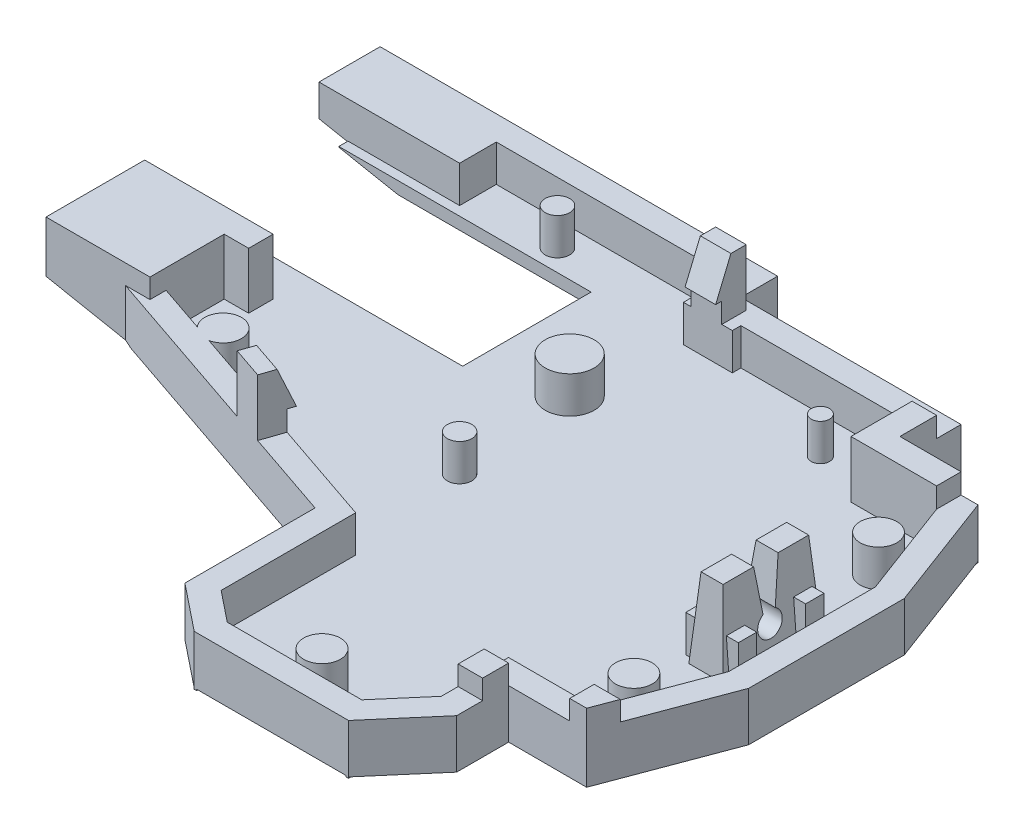
SolidWorks part; units mm, degrees
ref_plane "Front Plane" through (0, 0, 0) normal (0, 0, 1) x (1, 0, 0)
ref_plane "Top Plane" through (0, 0, 0) normal (0, 1, 0) x (1, 0, 0)
ref_plane "Right Plane" through (0, 0, 0) normal (1, 0, 0) x (0, 0, -1)
sketch "Sketch13" plane through (0, 0, 0) normal (0, 1, 0) x (1, 0, 0)
  line L1 (0, 0) -> (50, 0)
  line L2 (0, 0) -> (0, -45)
  line L3 (0, -45) -> (50, -45)
  line L4 (50, 0) -> (50, -45)
  dimension "D1" = 50
extrude "Boss-Extrude4" add sketch "Sketch13" along normal blind 1.6
sketch "Sketch14" plane through (0, 1.6, 0) normal (0, 1, 0) x (1, 0, 0)
  line L1 (50, 0) -> (40, 0)
  line L2 (50, 0) -> (50, -8)
  line L3 (50, -8) -> (40, -8)
  line L4 (40, 0) -> (40, -8)
extrude "Cut-Extrude6" cut sketch "Sketch14" against normal through all
sketch "Sketch15" plane through (0, 1.6, 0) normal (0, 1, 0) x (1, 0, 0)
  line L1 (40, 0) -> (22, 0)
  line L2 (40, 0) -> (40, -3)
  line L3 (40, -3) -> (22, -3)
  line L4 (22, 0) -> (22, -3)
extrude "Cut-Extrude7" cut sketch "Sketch15" against normal through all
sketch "Sketch16" plane through (0, 1.6, 0) normal (0, 1, 0) x (1, 0, 0)
  line L1 (22, -3) -> (26, -3)
  line L2 (22, -3) -> (22, -3.7)
  line L3 (22, -3.7) -> (26, -3.7)
  line L4 (26, -3) -> (26, -3.7)
  dimension "D1" = 0.7
  dimension "D2" = 4
extrude "Cut-Extrude8" cut sketch "Sketch16" against normal through all
sketch "Sketch17" plane through (0, 1.6, 0) normal (0, 1, 0) x (1, 0, 0)
  line L3 (40, -8) -> (50, -8) construction
  line L4 (47, -8) -> (50, -16)
  line L6 (50, -45) -> (50, -8) construction
  line L7 (50, -16) -> (65.8811, -16)
  line L8 (65.8811, -16) -> (65.8811, 17.9573)
  line L9 (65.8811, 17.9573) -> (47, 17.9573)
  line L10 (47, 17.9573) -> (47, -8)
extrude "Cut-Extrude9" cut sketch "Sketch17" against normal through all
sketch "Sketch18" plane through (0, 1.6, 0) normal (0, 1, 0) x (1, 0, 0)
  line L0 (40, -8) -> (40, -36) construction
  line L2 (40, -36) -> (61.1096, -36)
  line L3 (40, -36) -> (40, -58.8405)
  line L4 (40, -58.8405) -> (61.1096, -58.8405)
  line L5 (61.1096, -36) -> (61.1096, -58.8405)
extrude "Cut-Extrude10" cut sketch "Sketch18" against normal through all
sketch "Sketch21" plane through (0, 1.6, 0) normal (0, 1, 0) x (1, 0, 0)
  line L0 (50, -16) -> (27.9365, -16) construction
  line L1 (47, -36) -> (47, -28) construction
  line L2 (50, -36) -> (40, -36) construction
  line L3 (50, -28) -> (47, -36)
  line L4 (50, -36) -> (50, -16) construction
  line L5 (47, -36) -> (47, -49.2976)
  line L6 (47, -49.2976) -> (75.1968, -49.2976)
  line L7 (75.1968, -49.2976) -> (75.1968, -28)
  line L8 (75.1968, -28) -> (50, -28)
extrude "Cut-Extrude11" cut sketch "Sketch21" against normal through all
sketch "Sketch22" plane through (0, 1.6, 0) normal (0, 1, 0) x (1, 0, 0)
  line L0 (0, 0) -> (0, -19.3362) construction
  line L1 (0, 0) -> (0, -45) construction
  line L4 (0, -19.3362) -> (2, -19.3362)
  line L5 (0, -19.3362) -> (0, -22.3362)
  line L6 (0, -22.3362) -> (2, -22.3362)
  line L7 (2, -19.3362) -> (2, -22.3362)
  dimension "D1" = 2
  dimension "D2" = 3
extrude "Cut-Extrude12" cut sketch "Sketch22" against normal through all
sketch "Sketch23" plane through (0, 1.6, 0) normal (0, 1, 0) x (1, 0, 0)
  line L0 (40, -45) -> (23.5, -45) construction
  line L1 (0, -45) -> (40, -45) construction
  line L2 (23.5, -45) -> (23.5, -32)
  line L3 (0, -22.3362) -> (0, -26.3362) construction
  line L4 (0, -22.3362) -> (0, -45) construction
  line L5 (23.5, -32) -> (0, -26.3362)
  line L6 (0, -26.3362) -> (-30.2262, -26.3362)
  line L7 (-30.2262, -26.3362) -> (-30.2262, -63.1883)
  line L8 (-30.2262, -63.1883) -> (23.5, -63.1883)
  line L9 (23.5, -63.1883) -> (23.5, -45)
extrude "Cut-Extrude13" cut sketch "Sketch23" against normal through all
sketch "Sketch24" plane through (0, 1.6, 0) normal (0, 1, 0) x (1, 0, 0)
  line L0 (23.5, -43) -> (7.4911, -43)
  line L1 (23.5, -45) -> (40, -45) construction
  line L2 (7.4911, -43) -> (7.4911, -69.5502)
  line L3 (40, -36) -> (40, -45) construction
  line L4 (37, -45) -> (40, -41.5)
  line L5 (23.5, -45) -> (23.5, -32) construction
  line L6 (26, -45) -> (23.5, -43)
  line L7 (7.4911, -69.5502) -> (44.754, -69.5502)
  line L8 (44.754, -69.5502) -> (44.754, -41.5)
  line L9 (44.754, -41.5) -> (40, -41.5)
  line L10 (37, -45) -> (26, -45)
extrude "Cut-Extrude14" cut sketch "Sketch24" against normal through all
sketch "Sketch25" plane through (0, 1.6, 0) normal (0, 1, 0) x (1, 0, 0)
  line L0 (50, -22) -> (47.6007, -22.0598) construction
  line L1 (50, -28) -> (50, -16) construction
  line L2 (47.6007, -22.0598) -> (47.6007, -18.0598) construction
  line L4 (47.6007, -18.0598) -> (44.8007, -18.0598)
  line L5 (47.6007, -18.0598) -> (47.6007, -26.0598)
  line L6 (47.6007, -26.0598) -> (44.8007, -26.0598)
  line L7 (44.8007, -18.0598) -> (44.8007, -26.0598)
  dimension "D1" = 2.8
  dimension "D2" = 8
extrude "Cut-Extrude15" cut sketch "Sketch25" against normal through all
sketch "Sketch28" plane through (0, 0, 0) normal (0, -1, 0) x (1, 0, 0)
  line L44 (42, 38) -> (42, 42.2398)
  line L45 (42, 42.2398) -> (37.9199, 47)
  line L46 (37.9199, 47) -> (25.2984, 47)
  line L47 (25.2984, 47) -> (21.5, 43.9612)
  line L48 (21.5, 43.9612) -> (21.5, 33.5752)
  line L49 (21.5, 33.5752) -> (-2, 27.9115)
  line L50 (-2, 27.9115) -> (-2, -2)
  line L51 (-2, -2) -> (24, -2)
  line L52 (24, -2) -> (24, 1)
  line L53 (24, 1) -> (42, 1)
  line L54 (42, 1) -> (42, 6)
  line L55 (42, 6) -> (48.386, 6)
  line L56 (48.386, 6) -> (52, 15.6373)
  line L57 (52, 15.6373) -> (52, 28.3627)
  line L58 (52, 28.3627) -> (48.386, 38)
  line L59 (48.386, 38) -> (42, 38)
  line L60 (42, 38) -> (42, 42.2398)
  line L61 (42, 42.2398) -> (37.9199, 47)
  line L62 (37.9199, 47) -> (25.2984, 47)
  line L63 (25.2984, 47) -> (21.5, 43.9612)
  line L64 (21.5, 43.9612) -> (21.5, 33.5752)
  line L65 (21.5, 33.5752) -> (-2, 27.9115)
  line L66 (-2, 27.9115) -> (-2, -2)
  line L67 (-2, -2) -> (24, -2)
  line L68 (24, -2) -> (24, 1)
  line L69 (24, 1) -> (42, 1)
  line L70 (42, 1) -> (42, 6)
  line L71 (42, 6) -> (48.386, 6)
  line L72 (48.386, 6) -> (52, 15.6373)
  line L73 (52, 15.6373) -> (52, 28.3627)
  line L74 (52, 28.3627) -> (48.386, 38)
  line L75 (48.386, 38) -> (42, 38)
  dimension "D1" = 2
extrude "Boss-Extrude6" add sketch "Sketch28" along normal blind 6
sketch "Sketch30" plane through (0, 0, 0) normal (0, 1, 0) x (1, 0, 0)
  line L8 (44.8007, -18.0598) -> (44.8007, -26.0598)
  line L9 (44.8007, -26.0598) -> (47.6007, -26.0598)
  line L10 (47.6007, -26.0598) -> (47.6007, -18.0598)
  line L11 (47.6007, -18.0598) -> (44.8007, -18.0598)
  line L12 (44.8007, -18.0598) -> (44.8007, -26.0598)
  line L13 (44.8007, -26.0598) -> (47.6007, -26.0598)
  line L14 (47.6007, -26.0598) -> (47.6007, -18.0598)
  line L15 (47.6007, -18.0598) -> (44.8007, -18.0598)
  dimension "D1" = 0
extrude "Boss-Extrude7" add sketch "Sketch30" along normal blind 3.5
sketch "Sketch31" plane through (0, 1.6, 0) normal (0, 1, 0) x (1, 0, 0)
  line L44 (37, -45) -> (40, -41.5)
  line L45 (40, -41.5) -> (40, -36)
  line L46 (40, -36) -> (47, -36)
  line L47 (47, -36) -> (50, -28)
  line L48 (50, -28) -> (50, -16)
  line L49 (50, -16) -> (47, -8)
  line L50 (47, -8) -> (40, -8)
  line L51 (40, -8) -> (40, -3)
  line L52 (40, -3) -> (26, -3)
  line L53 (26, -3) -> (26, -3.7)
  line L54 (26, -3.7) -> (22, -3.7)
  line L55 (22, -3.7) -> (22, 0)
  line L56 (22, 0) -> (0, 0)
  line L57 (0, 0) -> (0, -19.3362)
  line L58 (0, -19.3362) -> (2, -19.3362)
  line L59 (2, -19.3362) -> (2, -22.3362)
  line L60 (2, -22.3362) -> (0, -22.3362)
  line L61 (0, -22.3362) -> (0, -26.3362)
  line L62 (0, -26.3362) -> (23.5, -32)
  line L63 (23.5, -32) -> (23.5, -43)
  line L64 (23.5, -43) -> (26, -45)
  line L65 (26, -45) -> (37, -45)
  line L66 (37, -45) -> (40, -41.5)
  line L67 (40, -41.5) -> (40, -36)
  line L68 (40, -36) -> (47, -36)
  line L69 (47, -36) -> (50, -28)
  line L70 (50, -28) -> (50, -16)
  line L71 (50, -16) -> (47, -8)
  line L72 (47, -8) -> (40, -8)
  line L73 (40, -8) -> (40, -3)
  line L74 (40, -3) -> (26, -3)
  line L75 (26, -3) -> (26, -3.7)
  line L76 (26, -3.7) -> (22, -3.7)
  line L77 (22, -3.7) -> (22, 0)
  line L78 (22, 0) -> (0, 0)
  line L79 (0, 0) -> (0, -19.3362)
  line L80 (0, -19.3362) -> (2, -19.3362)
  line L81 (2, -19.3362) -> (2, -22.3362)
  line L82 (2, -22.3362) -> (0, -22.3362)
  line L83 (0, -22.3362) -> (0, -26.3362)
  line L84 (0, -26.3362) -> (23.5, -32)
  line L85 (23.5, -32) -> (23.5, -43)
  line L86 (23.5, -43) -> (26, -45)
  line L87 (26, -45) -> (37, -45)
  dimension "D1" = 0
extrude "Cut-Extrude16" cut sketch "Sketch31" against normal blind 4.6
sketch "Sketch32" plane through (0, 1.6, 0) normal (0, -1, 0) x (1, 0, 0)
  line L8 (47.6007, 18.0598) -> (47.6007, 26.0598)
  line L9 (47.6007, 26.0598) -> (44.8007, 26.0598)
  line L10 (44.8007, 26.0598) -> (44.8007, 18.0598)
  line L11 (44.8007, 18.0598) -> (47.6007, 18.0598)
  line L12 (47.6007, 18.0598) -> (47.6007, 26.0598)
  line L13 (47.6007, 26.0598) -> (44.8007, 26.0598)
  line L14 (44.8007, 26.0598) -> (44.8007, 18.0598)
  line L15 (44.8007, 18.0598) -> (47.6007, 18.0598)
  dimension "D1" = 0
extrude "Boss-Extrude8" add sketch "Sketch32" along normal blind 4.6
sketch "Sketch35" plane through (47.6007, 0, 0) normal (1, 0, 0) x (0, 0, -1)
  line L0 (-22.0598, 3.5) -> (-22.0598, 0) construction
  line L1 (-26.0598, 3.5) -> (-18.0598, 3.5) construction
  line L2 (-22.0598, 3.5) -> (-21.0598, 3.5) construction
  line L3 (-22.0598, 3.5) -> (-23.0598, 3.5) construction
  line L4 (-22.0598, 0) -> (-21.5598, 0)
  line L5 (-21.5598, 0) -> (-21.0598, 3.5)
  line L6 (-22.0598, 0) -> (-22.5598, 0)
  line L7 (-22.5598, 0) -> (-23.0598, 3.5)
  line L8 (-23.0598, 3.5) -> (-23.2577, 4.8851)
  line L9 (-21.0598, 3.5) -> (-21.2977, 5.1651)
  line L10 (-21.2977, 5.1651) -> (-23.2577, 4.8851)
extrude "Cut-Extrude18" cut sketch "Sketch35" against normal blind 4.6
sketch "Sketch37" plane through (47.6007, 0, 0) normal (1, 0, 0) x (0, 0, -1)
  line L0 (-22.0598, 0) -> (-22.0598, -3.4808) construction
  line L1 (-22.5598, 0) -> (-21.5598, 0) construction
  line L2 (-21.5598, 0) -> (-22.0598, -0.866) construction
  circle A0 centre (-22.0598, -0.866) radius 1
extrude "Cut-Extrude19" cut sketch "Sketch37" against normal blind 4.6
sketch "Sketch39" plane through (44.8007, 0, 0) normal (-1, 0, 0) x (0, 0, 1)
  line L0 (26.0598, 3.5) -> (25.5598, 3.5) construction
  line L1 (23.0598, 3.5) -> (26.0598, 3.5) construction
  line L2 (25.5598, 3.5) -> (26.0598, -3)
  line L3 (26.0598, -3) -> (27.9064, -2.858)
  line L4 (27.9064, -2.858) -> (27.4064, 3.642)
  line L5 (27.4064, 3.642) -> (25.5598, 3.5)
  line L6 (18.0598, 3.5) -> (18.5598, 3.5) construction
  line L7 (18.0598, 3.5) -> (21.0598, 3.5) construction
  line L8 (18.5598, 3.5) -> (18.0598, -3)
  line L9 (18.0598, -3) -> (15.9573, -2.8383)
  line L10 (15.9573, -2.8383) -> (16.4557, 3.642)
  line L11 (16.4557, 3.642) -> (18.5598, 3.5)
extrude "Cut-Extrude20" cut sketch "Sketch39" against normal blind 4.6
sketch "Sketch41" plane through (0, 0, 0) normal (0, 0, 1) x (1, 0, 0)
  line L0 (44.8007, 3.5) -> (45.3007, 3.5) construction
  line L1 (44.8007, 3.5) -> (47.6007, 3.5) construction
  line L2 (47.6007, 3.5) -> (47.1007, 3.5) construction
  line L3 (45.3007, 3.5) -> (44.8007, -3)
  line L4 (44.8007, -3) -> (43.415, -2.8934)
  line L5 (43.415, -2.8934) -> (43.9406, 3.9398)
  line L6 (43.9406, 3.9398) -> (45.3007, 3.5)
  line L7 (47.1007, 3.5) -> (47.6007, -3)
  line L8 (47.6007, -3) -> (49.659, -2.8417)
  line L9 (49.659, -2.8417) -> (49.1373, 3.9398)
  line L10 (49.1373, 3.9398) -> (47.1007, 3.5)
extrude "Cut-Extrude21" cut sketch "Sketch41" along normal up to vertex
sketch "Sketch43" plane through (0, 0, 0) normal (0, 1, 0) x (1, 0, 0)
  line L0 (47, -8) -> (50, -16)
  line L1 (50, -16) -> (51.1704, -13.4251)
  line L2 (49.4404, -8.8117) -> (52, -15.6373) construction
  line L3 (46.2007, -6) -> (51.8278, -6) construction
  line L4 (45.0315, -6) -> (47.37, -6) construction
  line L5 (50.6159, -11.9464) -> (47.8466, -4.5615) construction
  line L6 (51.1704, -13.4251) -> (48.386, -6)
  line L7 (48.386, -6) -> (42.8188, -6)
  line L8 (42, -6) -> (43.6375, -6) construction
  line L9 (42.8188, -6) -> (42.8188, -8)
  line L10 (40, -8) -> (43.6375, -8) construction
  line L11 (42.8188, -8) -> (47, -8)
extrude "Boss-Extrude9" add sketch "Sketch43" against normal blind 4.6
sketch "Sketch44" plane through (0, -3, 0) normal (0, 1, 0) x (1, 0, 0)
  line L0 (47.6007, -18.0598) -> (47.6007, -18.5598) construction
  line L1 (47.6007, -18.0598) -> (47.6007, -26.0598) construction
  line L2 (47.6007, -18.5598) -> (48.3507, -18.5598) construction
  line L3 (44.8007, -18.5598) -> (44.0507, -18.5598) construction
  line L4 (44.8007, -26.0598) -> (44.8007, -18.0598) construction
  line L5 (47.6007, -26.0598) -> (47.6007, -25.5598) construction
  line L6 (48.3507, -25.5598) -> (44.0507, -25.5598) construction
  line L7 (48.3507, -18.5598) -> (48.3507, -20.0598)
  line L8 (48.3507, -25.5598) -> (48.3507, -24.0598)
  line L9 (48.3507, -24.0598) -> (44.0507, -24.0598)
  line L10 (44.0507, -24.0598) -> (44.0507, -25.5598)
  line L11 (44.0507, -25.5598) -> (48.3507, -25.5598)
  line L12 (48.3507, -20.0598) -> (44.0507, -20.0598)
  line L13 (44.0507, -20.0598) -> (44.0507, -18.5598)
  line L14 (44.0507, -18.5598) -> (48.3507, -18.5598)
extrude "Boss-Extrude11" add sketch "Sketch44" along normal blind 3
sketch "Sketch45" plane through (0, -3, 0) normal (0, 1, 0) x (1, 0, 0)
  line L0 (50, -22) -> (44, -22) construction
  line L1 (50, -28) -> (50, -16) construction
  line L2 (44, -22) -> (44, -32) construction
  line L3 (44, -32) -> (46.25, -32) construction
  line L4 (44, -22) -> (44, -12) construction
  line L5 (22, -3.7) -> (22, -22) construction
  line L6 (22, -22) -> (22, -21) construction
  line L7 (40, -36) -> (23.5, -36) construction
  line L8 (23.5, -32) -> (23.5, -43) construction
  line L9 (31.75, -45) -> (31.75, -43) construction
  line L10 (26, -45) -> (37, -45) construction
  line L11 (40, -3) -> (40, -6) construction
  line L12 (40, -8) -> (40, -3) construction
  line L13 (40, -6) -> (35.5, -6) construction
  line L14 (22, 0) -> (22, -2) construction
  line L15 (22, 0) -> (0, 0) construction
  line L16 (22, -3.7) -> (22, 0) construction
  line L17 (22, -2) -> (10, -2) construction
  line L18 (0, -24.3362) -> (5, -24.3362) construction
  line L19 (0, -22.3362) -> (0, -26.3362) construction
  circle A0 centre (46.25, -12) radius 1.5
  circle A1 centre (46.25, -32) radius 1.5
  circle A2 centre (22, -22) radius 1
  circle A3 centre (21, -12) radius 1.9996
  circle A4 centre (31.75, -43) radius 1.5033
  circle A5 centre (35.5, -6) radius 0.75
  circle A6 centre (10, -2) radius 1
  circle A7 centre (5, -24.3362) radius 1.5
extrude "Boss-Extrude12" add sketch "Sketch45" along normal blind 3
sketch "Sketch46" plane through (0, 0, 0) normal (0, 1, 0) x (1, 0, 0)
  line L0 (14.1373, -29.7435) -> (16.5677, -30.3292)
  line L1 (16.5677, -30.3292) -> (16.0991, -32.2736)
  line L2 (21.5, -33.5752) -> (-2, -27.9115) construction
  line L3 (16.0991, -32.2736) -> (13.6687, -31.6878)
  line L4 (13.6687, -31.6878) -> (14.1373, -29.7435)
  line L5 (24, -3.7) -> (25.1336, -3.7) construction
  line L6 (22, -3.7) -> (26, -3.7) construction
  line L7 (25.1336, -3.7) -> (22.6336, -3.7)
  line L8 (22.6336, -3.7) -> (22.6336, -1.7)
  line L9 (22.6336, -1.7) -> (25.1336, -1.7)
  line L10 (25.1336, -1.7) -> (25.1336, -3.7)
  line L11 (2, -20.8362) -> (2, -19.9327) construction
  line L12 (2, -22.3362) -> (2, -19.3362) construction
  line L13 (2, -19.9327) -> (2, -21.9327)
  line L14 (2, -21.9327) -> (0, -21.9327)
  line L15 (0, -21.9327) -> (0, -19.9327)
  line L16 (0, -19.9327) -> (2, -19.9327)
  line L17 (23.5, -32) -> (0, -26.3362) construction
  line L18 (16.5677, -30.3292) -> (14.1373, -29.7435) construction
  line L19 (47, -36) -> (48.8727, -36.7022)
  line L20 (52, -28.3627) -> (48.386, -38) construction
  line L21 (48.8727, -36.7022) -> (49.7505, -34.3614)
  line L22 (49.7505, -34.3614) -> (47.8778, -33.6592)
  line L23 (50, -28) -> (47, -36) construction
  line L24 (47.8778, -33.6592) -> (47, -36)
  line L25 (40, -3) -> (40, -8)
  line L26 (26, -3) -> (40, -3) construction
  line L27 (40, -3) -> (40, -8) construction
  line L28 (40, -8) -> (47, -8)
  line L29 (47, -8) -> (47, -6)
  line L30 (42, -6) -> (48.386, -6) construction
  line L31 (47, -6) -> (42, -6)
  line L32 (42, -6) -> (42, -3)
  line L33 (42, -1) -> (42, -6) construction
  line L34 (42, -3) -> (40, -3)
extrude "Boss-Extrude13" add sketch "Sketch46" along normal blind 1.65
sketch "Sketch47" plane through (0, 0, 0) normal (0, 1, 0) x (1, 0, 0)
  line L1 (0, 0) -> (3, 0)
  line L2 (0, 0) -> (0, -3)
  line L3 (0, -3) -> (3, -3)
  line L4 (3, 0) -> (3, -3)
extrude "Boss-Extrude14" add sketch "Sketch47" against normal up to surface (3 mm away) up to face at (10, -3, 3)
sketch "Sketch48" plane through (0, 0, 0) normal (0, 1, 0) x (1, 0, 0)
  line L0 (-2, -27.9115) -> (-2, 2) construction
  line L1 (0, -19.3362) -> (-2, -19.3362)
  line L2 (0, -19.3362) -> (0, -3)
  line L3 (0, -3) -> (-2, -3)
  line L4 (-2, -19.3362) -> (-2, -3)
extrude "Cut-Extrude22" cut sketch "Sketch48" against normal up to surface (3 mm away) up to face at (23.75, -3, 19.4826)
sketch "Sketch49" plane through (-2, 0, 0) normal (-1, 0, 0) x (0, 0, 1)
  line L1 (-2, -6) -> (19.3362, -6)
  line L2 (-2, -6) -> (-2, -3)
  line L3 (-2, -3) -> (19.3362, -3)
  line L4 (19.3362, -6) -> (19.3362, -3)
extrude "Boss-Extrude15" add sketch "Sketch49" along normal blind 13
sketch "Sketch50" plane through (0, -6, 0) normal (0, -1, 0) x (1, 0, 0)
  line L0 (52, 22) -> (52, -11.4177) construction
  line L1 (52, 15.6373) -> (52, 28.3627) construction
  line L2 (24, -2) -> (52, -2) construction
  line L3 (52, 22) -> (52, 58.8348) construction
  line L4 (34.4271, 47) -> (52, 47) construction
  line L5 (37.9199, 47) -> (25.2984, 47) construction
  line L7 (-15, -2) -> (52, -2)
  line L8 (-15, -2) -> (-15, 47)
  line L9 (-15, 47) -> (52, 47)
  line L10 (52, -2) -> (52, 47)
extrude "Boss-Extrude16" add sketch "Sketch50" against normal up to surface (3 mm away) up to face at (19.6296, -3, 17.9784)
sketch "Sketch51" plane through (0, -3, 0) normal (0, 1, 0) x (1, 0, 0)
  line L0 (47.6007, -26.0598) -> (47.6007, -47) construction
  line L1 (52, -47) -> (37.9199, -47) construction
  line L3 (47, -36) -> (52, -36)
  line L4 (47, -36) -> (47, -47)
  line L5 (47, -47) -> (52, -47)
  line L6 (52, -36) -> (52, -47)
extrude "Boss-Extrude17" add sketch "Sketch51" along normal blind 15.6
sketch "Sketch52" plane through (0, 1.65, 0) normal (0, 1, 0) x (1, 0, 0)
  line L8 (47.8778, -33.6592) -> (47, -36)
  line L9 (47, -36) -> (49.136, -36)
  line L10 (49.136, -36) -> (49.7505, -34.3614)
  line L11 (49.7505, -34.3614) -> (47.8778, -33.6592)
  line L12 (47.8778, -33.6592) -> (47, -36)
  line L13 (47, -36) -> (49.136, -36)
  line L14 (49.136, -36) -> (49.7505, -34.3614)
  line L15 (49.7505, -34.3614) -> (47.8778, -33.6592)
  dimension "D1" = 0
extrude "Cut-Extrude23" cut sketch "Sketch52" against normal up to surface (1.65 mm away) up to face at (49.3349, 0, 19.5578)
sketch "Sketch53" plane through (0, 0, 0) normal (0, 1, 0) x (1, 0, 0)
  line L0 (40, -36) -> (40, -41.5) construction
  line L1 (40, -37.9906) -> (42, -37.9906)
  line L2 (40, -37.9906) -> (40, -40.1199)
  line L3 (40, -40.1199) -> (42, -40.1199)
  line L4 (42, -37.9906) -> (42, -40.1199)
  line L5 (42, -38) -> (42, -42.2398) construction
extrude "Boss-Extrude18" add sketch "Sketch53" along normal blind 1.6
sketch "Sketch55" plane through (0, 1.65, 0) normal (0, 1, 0) x (1, 0, 0)
  line L1 (22.6336, -1.7) -> (25.1336, -1.7)
  line L2 (22.6336, -1.7) -> (22.6336, -4.2)
  line L3 (22.6336, -4.2) -> (25.1336, -4.2)
  line L4 (25.1336, -1.7) -> (25.1336, -4.2)
extrude "Boss-Extrude20" add sketch "Sketch55" along normal blind 3
sketch "Sketch56" plane through (25.1336, 0, 0) normal (1, 0, 0) x (0, 0, -1)
  line L0 (-4.2, 1.65) -> (-2.95, 4.65)
  line L1 (-4.2, 4.65) -> (-1.7, 4.65) construction
  line L2 (-2.95, 4.65) -> (-2.95, 7.6873)
  line L3 (-2.95, 7.6873) -> (-6.5972, 7.6873)
  line L4 (-6.5972, 7.6873) -> (-6.5972, 1.6413)
  line L5 (-6.5972, 1.6413) -> (-4.2, 1.65)
extrude "Cut-Extrude24" cut sketch "Sketch56" against normal blind 3
sketch "Sketch58" plane through (0, -3, 0) normal (0, 1, 0) x (1, 0, 0)
  line L0 (3, 0) -> (-15, 0) construction
  line L1 (-15, -47) -> (-15, 2) construction
  line L2 (0, -26.3362) -> (7.3396, -26.3362) construction
  line L3 (-15, -19.3362) -> (-15, -16.4918) construction
  line L4 (3, 0) -> (3, -3.75) construction
  line L5 (3, -3.75) -> (-5.5, -3.75) construction
  line L6 (-5.5, -3.75) -> (14.5, -3.75)
  line L7 (-5.5, -3.75) -> (-5.5, -14.25)
  line L8 (-5.5, -14.25) -> (14.5, -14.25)
  line L9 (14.5, -3.75) -> (14.5, -14.25)
  line L10 (7.3396, 0) -> (7.3396, -26.3362) construction
  line L11 (22, 0) -> (3, 0) construction
  line L12 (26, -45) -> (6.087, -45) construction
  line L13 (6.087, 0) -> (6.087, -45) construction
  line L14 (0, 0) -> (0, -25) construction
  line L15 (0, -22.3362) -> (0, -26.3362) construction
  line L16 (0, -14.25) -> (0, -17.2489) construction
  line L17 (2, -20.8362) -> (2, -17.2489) construction
  line L18 (2, -19.3362) -> (2, -22.3362) construction
  line L19 (0, -17.2489) -> (2, -17.2489)
  line L20 (2, -17.2489) -> (2, -19.2489)
  line L21 (2, -19.2489) -> (0, -19.2489)
  line L22 (0, -19.2489) -> (0, -17.2489)
extrude "Cut-Extrude29" cut sketch "Sketch58" against normal blind 1
sketch "Sketch60" plane through (0, -3, 0) normal (0, 1, 0) x (1, 0, 0)
  line L0 (27.9182, -45) -> (13.2629, -45) construction
  line L1 (26, -45) -> (37, -45) construction
  line L2 (23.5, -32) -> (23.5, -45) construction
  line L3 (0, 0) -> (0, -24) construction
  line L4 (0, -22.3362) -> (0, -26.3362) construction
  line L5 (0, -24) -> (23.5, -32)
  line L6 (23.5, -32) -> (0, -26.3362)
  line L7 (0, -26.3362) -> (23.5, -32) construction
  line L8 (0, -26.3362) -> (0, -24)
extrude "Boss-Extrude21" add sketch "Sketch60" along normal up to surface (3 mm away) up to face at (21.502, 0, 1.8353)
sketch "Sketch61" plane through (-5.9989, 0, 24.8904) normal (0.2343, 0, -0.9722) x (-0.9722, 0, -0.2343)
  line L8 (-23.2128, 1.65) -> (-23.2128, 0)
  line L9 (-23.2128, 0) -> (-20.7128, 0)
  line L10 (-20.7128, 0) -> (-20.7128, 1.65)
  line L11 (-20.7128, 1.65) -> (-23.2128, 1.65)
  line L12 (-23.2128, 1.65) -> (-23.2128, 0)
  line L13 (-23.2128, 0) -> (-20.7128, 0)
  line L14 (-20.7128, 0) -> (-20.7128, 1.65)
  line L15 (-20.7128, 1.65) -> (-23.2128, 1.65)
  dimension "D1" = 0
extrude "Boss-Extrude22" add sketch "Sketch61" along normal up to surface (0.8848 mm away)
sketch "Sketch62" plane through (0, 0, 0) normal (0, 1, 0) x (1, 0, 0)
  line L0 (0, -24) -> (0, -26) construction
  line L1 (1.9318, -24.6576) -> (-9.2599, -20.8477) construction
  line L2 (3.8635, -25.3152) -> (0, -24) construction
  line L3 (-9.2599, -20.8477) -> (-9.2599, -22.8477) construction
  line L4 (0, -26) -> (-0.5452, -28.2621)
  line L5 (13.6687, -31.6878) -> (-2, -27.9115) construction
  line L6 (-0.5452, -28.2621) -> (-9.9311, -26)
  line L7 (-9.9311, -26) -> (-9.2599, -22.8477)
  line L8 (-9.2599, -22.8477) -> (0, -26)
extrude "Cut-Extrude30" cut sketch "Sketch62" against normal up to surface (3 mm away) up to face at (35.5, -3, 6.75)
sketch "Sketch63" plane through (-6.4675, 0, 26.8348) normal (-0.2343, 0, 0.9722) x (0.9722, 0, 0.2343)
  line L16 (20.7128, 0) -> (6.0919, 0)
  line L17 (6.0919, 0) -> (6.0919, -3)
  line L18 (6.0919, -3) -> (28.7683, -3)
  line L19 (28.7683, -3) -> (28.7683, 0)
  line L20 (28.7683, 0) -> (23.2128, 0)
  line L21 (23.2128, 0) -> (23.2128, 1.65)
  line L22 (23.2128, 1.65) -> (20.7128, 1.65)
  line L23 (20.7128, 1.65) -> (20.7128, 0)
  line L24 (20.7128, 0) -> (6.0919, 0)
  line L25 (6.0919, 0) -> (6.0919, -3)
  line L26 (6.0919, -3) -> (28.7683, -3)
  line L27 (28.7683, -3) -> (28.7683, 0)
  line L28 (28.7683, 0) -> (23.2128, 0)
  line L29 (23.2128, 0) -> (23.2128, 1.65)
  line L30 (23.2128, 1.65) -> (20.7128, 1.65)
  line L31 (20.7128, 1.65) -> (20.7128, 0)
  dimension "D1" = 0
extrude "Cut-Extrude31" cut sketch "Sketch63" against normal up to surface (0.7539 mm away)
sketch "Sketch64" plane through (0, 1.65, 0) normal (0, 1, 0) x (1, 0, 0)
  line L0 (0, -21.9327) -> (0, -22.9624) construction
  line L2 (0, -22.9624) -> (2.5515, -22.9624)
  line L3 (0, -22.9624) -> (0, -18.6516)
  line L4 (0, -18.6516) -> (2.5515, -18.6516)
  line L5 (2.5515, -22.9624) -> (2.5515, -18.6516)
extrude "Cut-Extrude32" cut sketch "Sketch64" against normal up to surface (4.65 mm away) up to face at (18.4683, -3, 21.8358)
sketch "Sketch65" plane through (0, -4, 0) normal (0, 1, 0) x (1, 0, 0)
  line L8 (0, -17.2489) -> (0, -19.2489)
  line L9 (0, -19.2489) -> (2, -19.2489)
  line L10 (2, -19.2489) -> (2, -17.2489)
  line L11 (2, -17.2489) -> (0, -17.2489)
  line L12 (0, -17.2489) -> (0, -19.2489)
  line L13 (0, -19.2489) -> (2, -19.2489)
  line L14 (2, -19.2489) -> (2, -17.2489)
  line L15 (2, -17.2489) -> (0, -17.2489)
  dimension "D1" = 0
extrude "Boss-Extrude23" add sketch "Sketch65" along normal up to surface (4 mm away) up to face at (21.502, 0, 1.8353)
sketch "Sketch66" plane through (0, 0, 0) normal (0, 1, 0) x (1, 0, 0)
  line L1 (0, -19.2489) -> (2, -19.2489)
  line L2 (0, -19.2489) -> (0, -17.2489)
  line L3 (0, -17.2489) -> (2, -17.2489)
  line L4 (2, -19.2489) -> (2, -17.2489)
extrude "Boss-Extrude24" add sketch "Sketch66" along normal blind 1.6
sketch "Sketch67" plane through (0, 1.6, 0) normal (0, 1, 0) x (1, 0, 0)
  line L0 (0, -19.2489) -> (2.5, -19.2489)
  line L1 (0, -19.2489) -> (0, -17.2489)
  line L2 (0, -17.2489) -> (2.5, -17.2489)
  line L3 (2.5, -17.2489) -> (2.5, -19.2489)
extrude "Boss-Extrude25" add sketch "Sketch67" along normal blind 3
sketch "Sketch68" plane through (0, 0, 17.2489) normal (0, 0, -1) x (-1, 0, 0)
  line L0 (-2.5, 1.6) -> (-1.25, 4.6)
  line L1 (-2.5, 4.6) -> (0, 4.6) construction
  line L2 (-1.25, 4.6) -> (-1.25, 6.7749)
  line L3 (-1.25, 6.7749) -> (-4.4975, 6.7749)
  line L4 (-4.4975, 6.7749) -> (-4.4975, 1.5671)
  line L5 (-4.4975, 1.5671) -> (-2.5, 1.6)
extrude "Cut-Extrude33" cut sketch "Sketch68" against normal blind 3
sketch "Sketch69" plane through (0, 1.65, 0) normal (0, 1, 0) x (1, 0, 0)
  line L0 (14.3446, -28.8833) -> (16.7212, -29.6923) construction
  line L1 (16.7212, -29.6923) -> (18.8289, -30.4098) construction
  line L2 (16.2758, -31.5407) -> (16.8859, -29.7484) construction
  line L3 (16.2758, -31.5407) -> (16.7212, -29.6923) construction
  line L4 (16.2758, -31.5407) -> (13.8992, -30.7316) construction
  line L5 (14.3446, -28.8833) -> (16.8859, -29.7484)
  line L6 (16.8859, -29.7484) -> (16.2758, -31.5407)
  line L7 (16.2758, -31.5407) -> (12.9279, -30.401) construction
  line L8 (14.3446, -28.8833) -> (13.7345, -30.6756)
  line L9 (13.7345, -30.6756) -> (16.2758, -31.5407)
extrude "Boss-Extrude26" add sketch "Sketch69" against normal up to surface (1.65 mm away) up to face at (21.502, 0, 1.8353)
sketch "Sketch70" plane through (0, 0, 19.2489) normal (0, 0, 1) x (1, 0, 0)
  line L0 (2.5, 1.6) -> (1.25, 4.6) construction
  line L1 (2.5, 1.6) -> (-2.555, 1.6)
  line L2 (2.5, 1.6) -> (2.5, 7.1604)
  line L3 (2.5, 7.1604) -> (-2.555, 7.1604)
  line L4 (-2.555, 1.6) -> (-2.555, 7.1604)
extrude "Cut-Extrude34" cut sketch "Sketch70" against normal blind 3
sketch "Sketch71" plane through (0, 1.65, 0) normal (0, 1, 0) x (1, 0, 0)
  line L0 (16.2758, -31.5407) -> (17.0814, -29.1741)
  line L1 (16.2758, -31.5407) -> (13.7345, -30.6756)
  line L2 (18.2187, -25.945) -> (17.0814, -29.1741) construction
  line L3 (18.2187, -25.945) -> (16.2758, -31.5407) construction
  line L4 (17.0814, -29.1741) -> (11.4228, -27.2093) construction
  line L5 (13.7345, -30.6756) -> (14.5598, -28.2985)
  line L6 (14.5598, -28.2985) -> (17.0814, -29.1741)
extrude "Boss-Extrude27" add sketch "Sketch71" along normal blind 3
sketch "Sketch72" plane through (24.2076, 0, 8.2409) normal (0.9466, 0, 0.3223) x (0.3223, 0, -0.9466)
  line L0 (-22.1129, 1.65) -> (-23.3629, 4.65)
  line L1 (-24.6129, 4.65) -> (-22.1129, 4.65) construction
  line L2 (-23.3629, 4.65) -> (-23.3629, 7.6948)
  line L3 (-23.3629, 7.6948) -> (-20.7348, 7.6948)
  line L4 (-20.7348, 7.6948) -> (-20.7348, 1.65)
  line L5 (-20.7348, 1.65) -> (-22.1129, 1.65)
extrude "Cut-Extrude35" cut sketch "Sketch72" against normal blind 3
sketch "Sketch73" plane through (21.762, 0, 7.5561) normal (-0.9447, 0, -0.328) x (-0.328, 0, 0.9447)
  line L10 (24.4734, 4.65) -> (23.2234, 4.65)
  line L11 (23.2234, 4.65) -> (21.9734, 1.65)
  line L12 (21.9734, 1.65) -> (22.5801, 1.65)
  line L13 (22.5801, 1.65) -> (24.4734, 1.65)
  line L14 (24.4734, 1.65) -> (24.4734, 4.65)
  line L15 (24.4734, 4.65) -> (23.2234, 4.65)
  line L16 (23.2234, 4.65) -> (21.9734, 1.65)
  line L17 (21.9734, 1.65) -> (22.5801, 1.65)
  line L18 (22.5801, 1.65) -> (24.4734, 1.65)
  line L19 (24.4734, 1.65) -> (24.4734, 4.65)
  dimension "D1" = 0
extrude "Boss-Extrude28" add sketch "Sketch73" along normal up to surface (0.0115 mm away)
sketch "Sketch74" plane through (0, -4, 0) normal (0, 1, 0) x (1, 0, 0)
  line L0 (-5.5, -9) -> (14.5, -9) construction
  line L1 (-5.5, -3.75) -> (-5.5, -14.25) construction
  line L2 (14.5, -14.25) -> (14.5, -3.75) construction
  line L3 (-0.25, -6.1692) -> (-0.25, -11.6692) construction
  line L4 (4.5, -6.1692) -> (4.5, -11.6692) construction
  line L5 (-0.25, -6.1692) -> (9.25, -6.1692) construction
  line L6 (9.25, -6.1692) -> (9.25, -11.6692) construction
  line L7 (2.5808, -9) -> (-0.25, -6.1692) construction
  line L8 (6.4192, -6.1692) -> (2.5808, -6.1692)
  line L9 (9.25, -6.1692) -> (6.4192, -9) construction
  line L10 (6.4192, -11.8308) -> (2.5808, -11.8308)
  arc A0 (2.5808, -6.1692) -> (2.5808, -11.8308) centre (2.5808, -9) ccw
  arc A1 (6.4192, -6.1692) -> (6.4192, -11.8308) centre (6.4192, -9) cw
extrude "Cut-Extrude36" cut sketch "Sketch74" against normal blind 3
fillet "Fillet8" radius 1 4 edges at (-0.25, -6, 9) (4.5, -6, 6.1692) (9.25, -6, 9) (4.5, -6, 11.8308)
sketch "Sketch76" plane through (0, -3, 0) normal (0, 1, 0) x (1, 0, 0)
  line L0 (47, -47) -> (-8, -47) construction
  line L1 (25.2984, -47) -> (-15, -47) construction
  line L2 (-15, -47) -> (-15, -32.5)
  line L3 (-15, -47) -> (-15, 2) construction
  line L4 (-15, -32.5) -> (-8, -32.5)
  line L5 (-8, -32.5) -> (-8, -47)
  line L6 (-8, -47) -> (-15, -47)
extrude "Boss-Extrude29" add sketch "Sketch76" along normal blind 14.5
sketch "Sketch79" plane through (21.6663, 0, 7.3758) normal (-0.9466, 0, -0.3223) x (-0.3223, 0, 0.9466)
  line L12 (22.7196, 0) -> (24.6129, 0)
  line L13 (24.6129, 0) -> (24.6129, 4.65)
  line L14 (24.6129, 4.65) -> (23.3629, 4.65)
  line L15 (23.3629, 4.65) -> (22.1128, 1.65)
  line L16 (22.1128, 1.65) -> (22.7196, 1.65)
  line L17 (22.7196, 1.65) -> (22.7196, 0)
  line L18 (22.7196, 0) -> (24.6129, 0)
  line L19 (24.6129, 0) -> (24.6129, 4.65)
  line L20 (24.6129, 4.65) -> (23.3629, 4.65)
  line L21 (23.3629, 4.65) -> (22.1128, 1.65)
  line L22 (22.1128, 1.65) -> (22.7196, 1.65)
  line L23 (22.7196, 1.65) -> (22.7196, 0)
  dimension "D1" = 0
extrude "Boss-Extrude30" add sketch "Sketch79" along normal blind 2
sketch "Sketch80" plane through (24.2076, 0, 8.2409) normal (0.9466, 0, 0.3223) x (0.3223, 0, -0.9466)
  line L12 (-22.1129, 1.65) -> (-23.3629, 4.65)
  line L13 (-23.3629, 4.65) -> (-24.6129, 4.65)
  line L14 (-24.6129, 4.65) -> (-24.6129, 0)
  line L15 (-24.6129, 0) -> (-22.7196, 0)
  line L16 (-22.7196, 0) -> (-22.7196, 1.65)
  line L17 (-22.7196, 1.65) -> (-22.1129, 1.65)
  line L18 (-22.1129, 1.65) -> (-23.3629, 4.65)
  line L19 (-23.3629, 4.65) -> (-24.6129, 4.65)
  line L20 (-24.6129, 4.65) -> (-24.6129, 0)
  line L21 (-24.6129, 0) -> (-22.7196, 0)
  line L22 (-22.7196, 0) -> (-22.7196, 1.65)
  line L23 (-22.7196, 1.65) -> (-22.1129, 1.65)
  dimension "D1" = 0
extrude "Cut-Extrude37" cut sketch "Sketch80" against normal blind 2
sketch "Sketch83" plane through (19.773, 0, 6.7312) normal (-0.9466, 0, -0.3223) x (-0.3223, 0, 0.9466)
  line L12 (22.7196, 1.65) -> (22.7196, 0)
  line L13 (22.7196, 0) -> (24.6129, 0)
  line L14 (24.6129, 0) -> (24.6129, 4.65)
  line L15 (24.6129, 4.65) -> (23.3629, 4.65)
  line L16 (23.3629, 4.65) -> (22.1128, 1.65)
  line L17 (22.1128, 1.65) -> (22.7196, 1.65)
  line L18 (22.7196, 1.65) -> (22.7196, 0)
  line L19 (22.7196, 0) -> (24.6129, 0)
  line L20 (24.6129, 0) -> (24.6129, 4.65)
  line L21 (24.6129, 4.65) -> (23.3629, 4.65)
  line L22 (23.3629, 4.65) -> (22.1128, 1.65)
  line L23 (22.1128, 1.65) -> (22.7196, 1.65)
  dimension "D1" = 0
extrude "Boss-Extrude31" add sketch "Sketch83" against normal up to surface (2.6845 mm away) up to face at (14.7873, 2.1, 29.7071)
sketch "Sketch85" plane through (0, -3, 0) normal (0, 1, 0) x (1, 0, 0)
  line L1 (-8, -32.5) -> (22.5662, -32.5)
  line L2 (-8, -32.5) -> (-8, -34.2252)
  line L3 (-8, -34.2252) -> (22.5662, -34.2252)
  line L4 (22.5662, -32.5) -> (22.5662, -34.2252)
extrude "Boss-Extrude33" add sketch "Sketch85" along normal up to surface (3 mm away) up to face at (21.502, 0, 1.8353)
sketch "Sketch86" plane through (0, -3, 0) normal (0, 1, 0) x (1, 0, 0)
  line L10 (21.5, -43.9612) -> (21.5, -34.2252)
  line L11 (21.5, -34.2252) -> (-8, -34.2252)
  line L12 (-8, -34.2252) -> (-8, -47)
  line L13 (-8, -47) -> (25.2984, -47)
  line L14 (25.2984, -47) -> (21.5, -43.9612)
  line L15 (21.5, -43.9612) -> (21.5, -34.2252)
  line L16 (21.5, -34.2252) -> (-8, -34.2252)
  line L17 (-8, -34.2252) -> (-8, -47)
  line L18 (-8, -47) -> (25.2984, -47)
  line L19 (25.2984, -47) -> (21.5, -43.9612)
  dimension "D1" = 0
extrude "Boss-Extrude34" add sketch "Sketch86" along normal up to surface (3 mm away) up to face at (21.502, 0, 1.8353)
sketch "Sketch87" plane through (0, -3, 0) normal (0, 1, 0) x (1, 0, 0)
  line L10 (37.9199, -47) -> (47, -47)
  line L11 (47, -47) -> (47, -38)
  line L12 (47, -38) -> (42, -38)
  line L13 (42, -38) -> (42, -42.2398)
  line L14 (42, -42.2398) -> (37.9199, -47)
  line L15 (37.9199, -47) -> (47, -47)
  line L16 (47, -47) -> (47, -38)
  line L17 (47, -38) -> (42, -38)
  line L18 (42, -38) -> (42, -42.2398)
  line L19 (42, -42.2398) -> (37.9199, -47)
  dimension "D1" = 0
extrude "Boss-Extrude35" add sketch "Sketch87" along normal up to surface (3 mm away) up to face at (21.502, 0, 1.8353)
sketch "Sketch88" plane through (0, 0, 0) normal (0, 1, 0) x (1, 0, 0)
  line L1 (-8, -47) -> (19.0938, -47)
  line L2 (-8, -47) -> (-8, -32.5)
  line L3 (-8, -32.5) -> (19.0938, -32.5)
  line L4 (19.0938, -47) -> (19.0938, -32.5)
extrude "Boss-Extrude36" add sketch "Sketch88" along normal blind 1.6
sketch "Sketch90" plane through (0, 11.5, 0) normal (0, 1, 0) x (1, 0, 0)
  line L8 (-15, -47) -> (-8, -47)
  line L9 (-8, -47) -> (-8, -32.5)
  line L10 (-8, -32.5) -> (-15, -32.5)
  line L11 (-15, -32.5) -> (-15, -47)
  line L12 (-15, -47) -> (-8, -47)
  line L13 (-8, -47) -> (-8, -32.5)
  line L14 (-8, -32.5) -> (-15, -32.5)
  line L15 (-15, -32.5) -> (-15, -47)
  dimension "D1" = 0
extrude "Boss-Extrude37" add sketch "Sketch90" along normal blind 1.6
sketch "Sketch93" plane through (0, 12.6, 0) normal (0, 1, 0) x (1, 0, 0)
  line L1 (47, -47) -> (52, -47)
  line L2 (47, -47) -> (47, -36)
  line L3 (47, -36) -> (52, -36)
  line L4 (52, -47) -> (52, -36)
extrude "Boss-Extrude38" add sketch "Sketch93" along normal blind 0.5
sketch "Sketch94" plane through (0, -3, 0) normal (0, 1, 0) x (1, 0, 0)
  line L0 (19.0938, -32.5) -> (-15, -32.5) construction
  line L1 (1.1186, -32.5) -> (9.7243, -32.5)
  line L2 (1.1186, -32.5) -> (1.1186, -30.5)
  line L3 (1.1186, -30.5) -> (9.7243, -30.5)
  line L4 (9.7243, -32.5) -> (9.7243, -30.5)
  dimension "D1" = 2
extrude "Boss-Extrude39" add sketch "Sketch94" along normal blind 15.6
sketch "Sketch96" plane through (0, 12.6, 0) normal (0, 1, 0) x (1, 0, 0)
  line L8 (1.1186, -30.5) -> (1.1186, -32.5)
  line L9 (1.1186, -32.5) -> (9.7243, -32.5)
  line L10 (9.7243, -32.5) -> (9.7243, -30.5)
  line L11 (9.7243, -30.5) -> (1.1186, -30.5)
  line L12 (1.1186, -30.5) -> (1.1186, -32.5)
  line L13 (1.1186, -32.5) -> (9.7243, -32.5)
  line L14 (9.7243, -32.5) -> (9.7243, -30.5)
  line L15 (9.7243, -30.5) -> (1.1186, -30.5)
  dimension "D1" = 0
extrude "Boss-Extrude40" add sketch "Sketch96" along normal blind 0.5
sketch "Sketch97" plane through (0, -6, 0) normal (0, -1, 0) x (1, 0, 0)
  line L1 (-15, 47) -> (-17, 47)
  line L2 (-15, 47) -> (-15, -2)
  line L3 (-15, -2) -> (-17, -2)
  line L4 (-17, 47) -> (-17, -2)
  dimension "D1" = 2
extrude "Boss-Extrude41" add sketch "Sketch97" against normal up to surface (19.1 mm away) up to face at (-11.5, 13.1, 39.75)
sketch "Sketch98" plane through (0, -6, 0) normal (0, -1, 0) x (1, 0, 0)
  line L1 (-17, 47) -> (52, 47)
  line L2 (-17, 47) -> (-17, 49)
  line L3 (-17, 49) -> (52, 49)
  line L4 (52, 47) -> (52, 49)
  dimension "D1" = 2
extrude "Boss-Extrude42" add sketch "Sketch98" against normal up to surface (19.1 mm away) up to face at (-12.75, 13.1, 22.9583)
sketch "Sketch99" plane through (0, 0, 19.3362) normal (0, 0, -1) x (-1, 0, 0)
  line L8 (2, 0) -> (0, 0)
  line L9 (0, 0) -> (0, -3)
  line L10 (0, -3) -> (2, -3)
  line L11 (2, -3) -> (2, 0)
  line L12 (2, 0) -> (0, 0)
  line L13 (0, 0) -> (0, -3)
  line L14 (0, -3) -> (2, -3)
  line L15 (2, -3) -> (2, 0)
  dimension "D1" = 0
extrude "Boss-Extrude43" add sketch "Sketch99" along normal up to surface (2.0874 mm away) up to face at (0.75, -0.125, 17.2489)
sketch "Sketch100" plane through (0, -6, 0) normal (0, -1, 0) x (1, 0, 0)
  line L1 (52, 49) -> (54, 49)
  line L2 (52, 49) -> (52, -2)
  line L3 (52, -2) -> (54, -2)
  line L4 (54, 49) -> (54, -2)
  dimension "D1" = 2
extrude "Boss-Extrude45" add sketch "Sketch100" against normal up to surface (19.1 mm away) up to face at (9.4, 13.1, 30.95)
sketch "Sketch101" plane through (0, -6, 0) normal (0, -1, 0) x (1, 0, 0)
  line L1 (54, -2) -> (-17, -2)
  line L2 (54, -2) -> (54, -4)
  line L3 (54, -4) -> (-17, -4)
  line L4 (-17, -2) -> (-17, -4)
  dimension "D1" = 2
extrude "Boss-Extrude46" add sketch "Sketch101" against normal up to surface (19.1 mm away) up to face at (17.0417, 13.1, 27.0417)
sketch "Sketch102" plane through (0, -3, 0) normal (0, 1, 0) x (1, 0, 0)
  line L0 (24, 2) -> (52, 2) construction
  line L1 (52, 2) -> (52, -15.6373) construction
  line L2 (52, 0) -> (50, 0) construction
  line L3 (50, 2) -> (50, 2.8367)
  line L4 (50, 2.8367) -> (52.9285, 2.8367)
  line L5 (52.9285, 2.8367) -> (52.9285, 0)
  line L6 (52.9285, 0) -> (52, 0)
  arc A0 (52, 0) -> (50, 2) centre (50, 0) ccw
extrude "Boss-Extrude47" add sketch "Sketch102" along normal up to surface (16.1 mm away)
sketch "Sketch103" plane through (0, -3, 0) normal (0, 1, 0) x (1, 0, 0)
  line L0 (-15, 2) -> (-13, 2) construction
  line L1 (-15, 2) -> (-2, 2) construction
  line L2 (-13, 2) -> (-13, 0) construction
  line L3 (-15, -32.5) -> (-15, 2) construction
  line L4 (-13, 2) -> (-13, 3.3193)
  line L5 (-13, 3.3193) -> (-16.3151, 3.3193)
  line L6 (-16.3151, 3.3193) -> (-16.3151, 0)
  line L7 (-16.3151, 0) -> (-15, 0)
  arc A0 (-13, 2) -> (-15, 0) centre (-13, 0) ccw
extrude "Boss-Extrude48" add sketch "Sketch103" along normal up to surface (16.1 mm away)
fillet "Fillet9" radius 2 8 edges at (18.5, -6, 49) (54, -6, 22.5) (18.5, -6, -4) (-17, -6, 22.5) (-17, 3.55, 49) (54, 3.55, 49) (54, 3.55, -4) (-17, 3.55, -4)
sketch "Sketch105" plane through (0, 13.1, 0) normal (0, 1, 0) x (1, 0, 0)
  line L8 (-16, 2) -> (-16, -47)
  line L9 (-15, -48) -> (52, -48)
  line L10 (53, -47) -> (53, 2)
  line L11 (52, 3) -> (-15, 3)
  line L12 (-16, 2) -> (-16, -47)
  line L13 (-15, -48) -> (52, -48)
  line L14 (53, -47) -> (53, 2)
  line L15 (52, 3) -> (-15, 3)
  arc A8 (-16, -47) -> (-15, -48) centre (-15, -47) ccw
  arc A9 (52, -48) -> (53, -47) centre (52, -47) ccw
  arc A10 (53, 2) -> (52, 3) centre (52, 2) ccw
  arc A11 (-15, 3) -> (-16, 2) centre (-15, 2) ccw
  arc A12 (-16, -47) -> (-15, -48) centre (-15, -47) ccw
  arc A13 (52, -48) -> (53, -47) centre (52, -47) ccw
  arc A14 (53, 2) -> (52, 3) centre (52, 2) ccw
  arc A15 (-15, 3) -> (-16, 2) centre (-15, 2) ccw
  dimension "D1" = 1
extrude "Cut-Extrude38" cut sketch "Sketch105" against normal blind 3 flip side to cut
sketch "Sketch106" plane through (0, -6, 0) normal (0, -1, 0) x (1, 0, 0)
  line L92 (-2, -2) -> (24, -2)
  line L93 (24, -2) -> (24, 1)
  line L94 (24, 1) -> (42, 1)
  line L95 (42, 1) -> (42, 6)
  line L96 (42, 6) -> (48.386, 6)
  line L97 (48.386, 6) -> (52, 15.6373)
  line L98 (52, 15.6373) -> (52, 28.3627)
  line L99 (52, 28.3627) -> (49.136, 36)
  line L100 (42, 40.81) -> (42, 43.4756) construction
  line L102 (40, 40.81) -> (42, 40.81) construction
  line L103 (40, 40.1199) -> (40, 41.5) construction
  line L104 (38.5, 43.25) -> (40.0185, 44.5516) construction
  line L105 (40, 41.5) -> (37, 45) construction
  line L106 (31.5, 45) -> (31.5, 47) construction
  line L107 (26, 45) -> (37, 45) construction
  line L108 (21.5, 33.3191) -> (-2, 25.3191)
  line L110 (-2, 25.3191) -> (-2, 17.2489)
  line L112 (21.5, 33.3191) -> (21.5, 43.9612)
  line L113 (49.136, 36) -> (48.386, 38)
  line L114 (48.386, 38) -> (42, 37.9906)
  line L115 (42, 42.2398) -> (37.9199, 47) construction
  line L116 (-8, 47) -> (47, 47) construction
  line L118 (23.5006, 45.5617) -> (21.5, 43.9612) construction
  line L119 (21.5, 38.4892) -> (21.5, 43.9612) construction
  line L120 (21.5, 43.9612) -> (25.2984, 47)
  line L121 (25.2984, 47) -> (37.9199, 47)
  line L122 (37.9199, 47) -> (42, 42.2398)
  line L123 (42, 42.2398) -> (42, 37.9906)
  line L124 (-2, 17.2489) -> (-8.3721, 17.2489)
  line L125 (-2, 3) -> (-2, -2)
  line L126 (-8.3721, 17.2489) -> (-8.3721, 3)
  line L127 (-8.3721, 3) -> (-2, 3)
  line L129 (56.2206, 50.8933) -> (-20.8354, 50.8933)
  line L130 (56.2206, 50.8933) -> (56.2206, -7.6303)
  line L131 (56.2206, -7.6303) -> (-20.8354, -7.6303)
  line L132 (-20.8354, 50.8933) -> (-20.8354, -7.6303)
extrude "Cut-Extrude39" cut sketch "Sketch106" against normal through all
sketch "Sketch107" plane through (0, 13.1, 0) normal (0, 1, 0) x (1, 0, 0)
  line L1 (51.4721, -35.1845) -> (38.0965, -35.1845)
  line L2 (51.4721, -35.1845) -> (51.4721, -41.3641)
  line L3 (51.4721, -41.3641) -> (38.0965, -41.3641)
  line L4 (38.0965, -35.1845) -> (38.0965, -41.3641)
extrude "Cut-Extrude40" cut sketch "Sketch107" against normal up to surface (11.5 mm away) up to face at (41, 1.6, 39.0552)
sketch "Sketch111" plane through (0, -4, 0) normal (0, 1, 0) x (1, 0, 0)
  circle A0 centre (2.5808, -9) radius 2.8308
sketch "Sketch113" plane through (0, -3, 0) normal (0, 1, 0) x (1, 0, 0)
  line L0 (-6.1286, -3) -> (-6.1286, -14.8614)
  line L1 (-2, -3) -> (-8.3721, -3) construction
  line L2 (-6.1286, -14.8614) -> (-2, -14.8614)
  line L3 (-2, -14.8614) -> (-2, -17.2489)
  line L4 (-2, -17.2489) -> (-9.2465, -26.4524)
  line L5 (-9.2465, -26.4524) -> (-13.8144, -0.6572)
  line L6 (-13.8144, -0.6572) -> (-2.9741, 6.6898)
  line L7 (-2.9741, 6.6898) -> (-3.5377, 5.9741)
  line L8 (-3.5377, 5.9741) -> (-6.1286, -3)
extrude "Cut-Extrude41" cut sketch "Sketch113" against normal through all
sketch "Sketch114" plane through (0, -6, 0) normal (0, -1, 0) x (1, 0, 0)
  line L1 (-8.5229, -3.0253) -> (57.814, -3.0253)
  line L2 (-8.5229, -3.0253) -> (-8.5229, 48.6433)
  line L3 (-8.5229, 48.6433) -> (57.814, 48.6433)
  line L4 (57.814, -3.0253) -> (57.814, 48.6433)
extrude "Cut-Extrude42" cut sketch "Sketch114" against normal up to surface (2 mm away) up to face at (4.5, -4, 9)
sketch "Sketch115" plane through (-2, 0, 0) normal (-1, 0, 0) x (0, 0, 1)
  line L12 (14.8614, -3) -> (14.8614, -4)
  line L13 (14.8614, -4) -> (25.3191, -4)
  line L14 (25.3191, -4) -> (25.3191, 0)
  line L15 (25.3191, 0) -> (17.2489, 0)
  line L16 (17.2489, 0) -> (17.2489, -3)
  line L17 (17.2489, -3) -> (14.8614, -3)
  line L18 (14.8614, -3) -> (14.8614, -4)
  line L19 (14.8614, -4) -> (25.3191, -4)
  line L20 (25.3191, -4) -> (25.3191, 0)
  line L21 (25.3191, 0) -> (17.2489, 0)
  line L22 (17.2489, 0) -> (17.2489, -3)
  line L23 (17.2489, -3) -> (14.8614, -3)
  line L28 (-2, 0) -> (-2, -4)
  line L29 (-2, -4) -> (3, -4)
  line L30 (3, -4) -> (3, -3)
  line L31 (3, -3) -> (3, 0)
  line L32 (3, 0) -> (-2, 0)
  line L33 (-2, 0) -> (-2, -4)
  line L34 (-2, -4) -> (3, -4)
  line L35 (3, -4) -> (3, -3)
  line L36 (3, -3) -> (3, 0)
  line L37 (3, 0) -> (-2, 0)
  dimension "D1" = 0
  dimension "D2" = 0
extrude "Boss-Extrude49" add sketch "Sketch115" along normal blind 6.5
sketch "Sketch116" plane through (0, -3, 0) normal (0, 1, 0) x (1, 0, 0)
  line L0 (-6.1286, -14.8614) -> (-6.1286, -3) construction
  line L1 (-5.5, -3.75) -> (-6.1286, -3.75)
  line L2 (-5.5, -3.75) -> (-5.5, -14.25)
  line L3 (-5.5, -14.25) -> (-6.1286, -14.25)
  line L4 (-6.1286, -3.75) -> (-6.1286, -14.25)
extrude "Cut-Extrude43" cut sketch "Sketch116" against normal blind 6.5
sketch "Sketch117" plane through (0, 0, 0) normal (0, 1, 0) x (1, 0, 0)
  line L1 (-8.5, -25.3191) -> (0, -25.3191)
  line L2 (-8.5, -25.3191) -> (-8.5, -17.2489)
  line L3 (-8.5, -17.2489) -> (0, -17.2489)
  line L4 (0, -25.3191) -> (0, -17.2489)
extrude "Boss-Extrude50" add sketch "Sketch117" along normal up to surface (1.6 mm away) up to face at (0.5, 1.6, 18.4989)
sketch "Sketch118" plane through (0, -4, 0) normal (0, -1, 0) x (1, 0, 0)
  line L0 (-6.1286, 14.25) -> (-6.6286, 14.25)
  line L1 (-6.6286, 14.25) -> (-6.6286, 3.6453)
sketch "Sketch119" plane through (0, 0, 25.3191) normal (0, 0, 1) x (1, 0, 0)
  line L0 (-8.5, -2.6) -> (-1.2976, -4) construction
  line L1 (-8.5, -4) -> (-8.5, 1.6) construction
  line L2 (5.4117, -4) -> (-0.25, -4) construction
  dimension "D1" = 1.4
  dimension "D2" = 7.2024
sketch "Sketch120" plane through (-8.5, 0, 0) normal (-1, 0, 0) x (0, 0, 1)
  line L0 (25.3191, -2.6) -> (-2, -2.6) construction
  line L1 (-2, 0) -> (-2, -4) construction
ref_plane "Plane1" through (-0.7965, -4.0974, 0) normal (0.1908, 0.9816, 0) x (0.9816, -0.1908, 0)
sketch "Sketch121" plane through (-0.7965, -4.0974, 0) normal (0.1908, 0.9816, 0) x (0.9816, -0.1908, 0)
  line L1 (19.9362, -78.5281) -> (-22.0114, -78.5281)
  line L2 (19.9362, -78.5281) -> (19.9362, 26.0108)
  line L3 (19.9362, 26.0108) -> (-22.0114, 26.0108)
  line L4 (-22.0114, -78.5281) -> (-22.0114, 26.0108)
  line L5 (19.9362, -78.5281) -> (-22.0114, 26.0108) construction
  line L6 (19.9362, 26.0108) -> (-22.0114, -78.5281) construction
  point P0 (-1.0376, -26.2587)
extrude "Cut-Extrude44" cut sketch "Sketch121" against normal through all
sketch "Sketch122" plane through (0, -4, 0) normal (0, -1, 0) x (1, 0, 0)
  line L1 (42, 1) -> (41.8, 1)
  line L2 (42, 1) -> (42, 1.2)
  line L3 (42, 1.2) -> (41.8, 1.2)
  line L4 (41.8, 1) -> (41.8, 1.2)
  line L5 (48.386, 6) -> (48.186, 6)
  line L6 (48.386, 6) -> (48.386, 6.2)
  line L7 (48.386, 6.2) -> (48.186, 6.2)
  line L8 (48.186, 6) -> (48.186, 6.2)
  line L9 (25.2984, 47) -> (25.4984, 47)
  line L10 (25.2984, 47) -> (25.2984, 46.8)
  line L11 (25.2984, 46.8) -> (25.4984, 46.8)
  line L12 (25.4984, 47) -> (25.4984, 46.8)
  line L13 (37.9199, 47) -> (37.7199, 47)
  line L14 (37.9199, 47) -> (37.9199, 46.8)
  line L15 (37.9199, 46.8) -> (37.7199, 46.8)
  line L16 (37.7199, 47) -> (37.7199, 46.8)
  dimension "D1" = 0.2
  dimension "D2" = 0.2
  dimension "D3" = 0.2
  dimension "D4" = 0.2
extrude "Boss-Extrude51" add sketch "Sketch122" along normal blind 0.1
